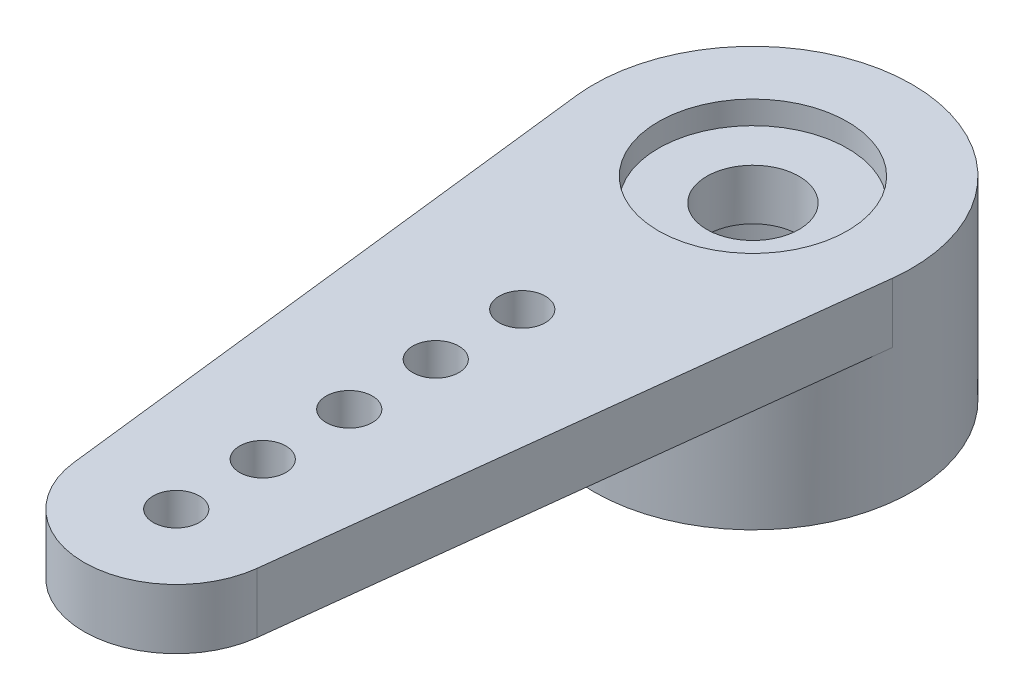
SolidWorks part; units mm, degrees
material "ABS"
ref_plane "Front Plane" through (0, 0, 0) normal (0, 0, 1) x (1, 0, 0)
ref_plane "Top Plane" through (0, 0, 0) normal (0, 1, 0) x (1, 0, 0)
ref_plane "Right Plane" through (0, 0, 0) normal (1, 0, 0) x (0, 0, -1)
sketch "Sketch1" plane through (0, 0, 0) normal (0, 1, 0) x (1, 0, 0)
  circle A0 centre (0, 0) radius 3.45
  dimension "D1" = 6.9
extrude "Boss-Extrude1" add sketch "Sketch1" along normal blind 4.2
sketch "Sketch3" plane through (0, 4.2, 0) normal (0, 1, 0) x (1, 0, 0)
  line L0 (-3.4267, -0.4002) -> (-1.9865, -12.732)
  line L1 (1.9865, -12.732) -> (3.4267, -0.4002)
  line L2 (0, 0) -> (0, -12.5) construction
  circle A0 centre (0, 0) radius 3.45 construction
  arc A1 (-1.9865, -12.732) -> (1.9865, -12.732) centre (0, -12.5) ccw
  arc A2 (-3.4267, -0.4002) -> (3.4267, -0.4002) centre (0, 0) cw
  dimension "D2" = 2
  dimension "D1" = 12.5
extrude "Boss-Extrude2" add sketch "Sketch3" against normal blind 1.3
sketch "Sketch2" plane through (0, 4.2, 0) normal (0, 1, 0) x (1, 0, 0)
  circle A0 centre (0, 0) radius 2.05
  dimension "D1" = 4.1
extrude "Cut-Extrude1" cut sketch "Sketch2" against normal blind 0.5
sketch "Sketch4" plane through (0, 4.2, 0) normal (0, 1, 0) x (1, 0, 0)
  line L0 (0, -5) -> (0, -6.875) construction
  line L1 (0, -6.875) -> (0, -8.75) construction
  line L2 (0, -8.75) -> (0, -10.625) construction
  line L3 (0, -10.625) -> (0, -12.5) construction
  circle A0 centre (0, -12.5) radius 0.5
  circle A1 centre (0, -10.625) radius 0.5
  circle A2 centre (0, -8.75) radius 0.5
  circle A3 centre (0, -6.875) radius 0.5
  circle A4 centre (0, -5) radius 0.5
  dimension "D1" = 1
  dimension "D2" = 7.5
extrude "Cut-Extrude2" cut sketch "Sketch4" against normal through all
sketch "Sketch5" plane through (0, 3.7, 0) normal (0, 1, 0) x (1, 0, 0)
  circle A0 centre (0, 0) radius 1
  dimension "D1" = 2
extrude "Cut-Extrude3" cut sketch "Sketch5" against normal through all
sketch "Sketch6" plane through (0, 0, 0) normal (0, -1, 0) x (1, 0, 0)
  circle A0 centre (0, 0) radius 2.5
  circle A1 centre (0, 0) radius 2.3 construction
  dimension "D1" = 5
  dimension "D2" = 0.2
extrude "Cut-Extrude4" cut sketch "Sketch6" against normal blind 2.6
